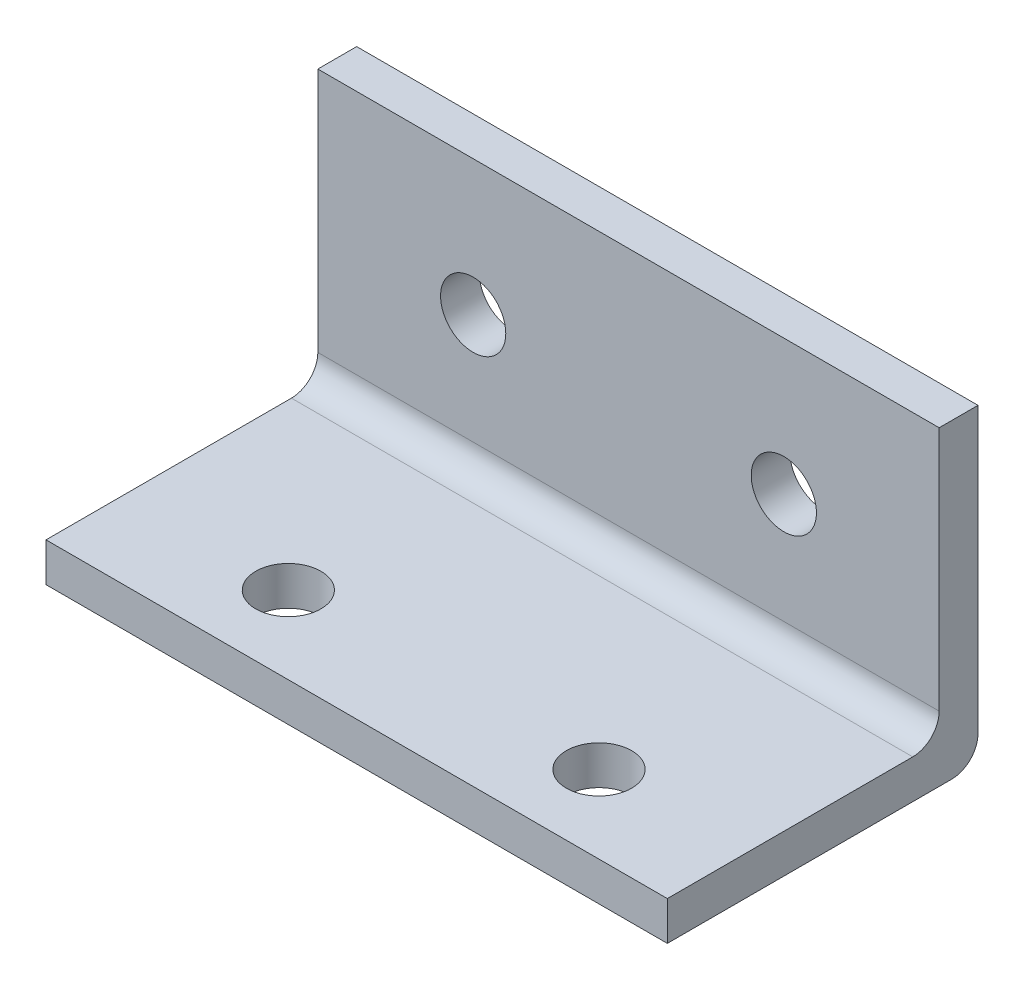
SolidWorks part; units mm, degrees
ref_plane "Front Plane" through (0, 0, 0) normal (0, 0, 1) x (1, 0, 0)
ref_plane "Top Plane" through (0, 0, 0) normal (0, 1, 0) x (1, 0, 0)
ref_plane "Right Plane" through (0, 0, 0) normal (1, 0, 0) x (0, 0, -1)
sketch "Sketch1" plane through (0, 0, 0) normal (1, 0, 0) x (0, 0, -1)
  line L0 (0, 0) -> (0, 25.4)
  line L1 (0, 0) -> (-25.4, 0)
  line L2 (-25.4, 0) -> (-25.4, 3.175)
  line L3 (-25.4, 3.175) -> (-3.175, 3.175)
  line L4 (-3.175, 3.175) -> (-3.175, 25.4)
  line L5 (-3.175, 25.4) -> (0, 25.4)
extrude "Boss-Extrude1" add sketch "Sketch1" along normal blind 50.8
sketch "Sketch2" plane through (0, 3.175, 0) normal (0, 1, 0) x (1, 0, 0)
  line L0 (0, 0) -> (0, -19.05)
  line L1 (0, -3.175) -> (0, -25.4) construction
  line L2 (0, -19.05) -> (13.462, -19.05)
  circle A0 centre (13.462, -19.05) radius 2.667
  circle A1 centre (38.862, -19.05) radius 2.667
  dimension "D1" = 2
extrude "Cut-Extrude1" cut sketch "Sketch2" against normal up to surface (3.175 mm away) up to face at (25.4, 0, 12.7)
sketch "Sketch3" plane through (0, 0, 3.175) normal (0, 0, 1) x (1, 0, 0)
  line L0 (50.8, 0) -> (50.8, 14.351)
  line L1 (50.8, 25.4) -> (50.8, 3.175) construction
  line L2 (50.8, 14.351) -> (38.1, 14.351)
  circle A0 centre (38.1, 14.351) radius 2.667
  circle A1 centre (12.7, 14.351) radius 2.667
  dimension "D1" = 2
extrude "Cut-Extrude2" cut sketch "Sketch3" against normal up to surface (3.175 mm away) up to face at (25.4, 12.7, 0)
fillet "Fillet1" radius 2.159 2 edges at (25.4, 0, 0) (25.4, 3.175, 3.175)
